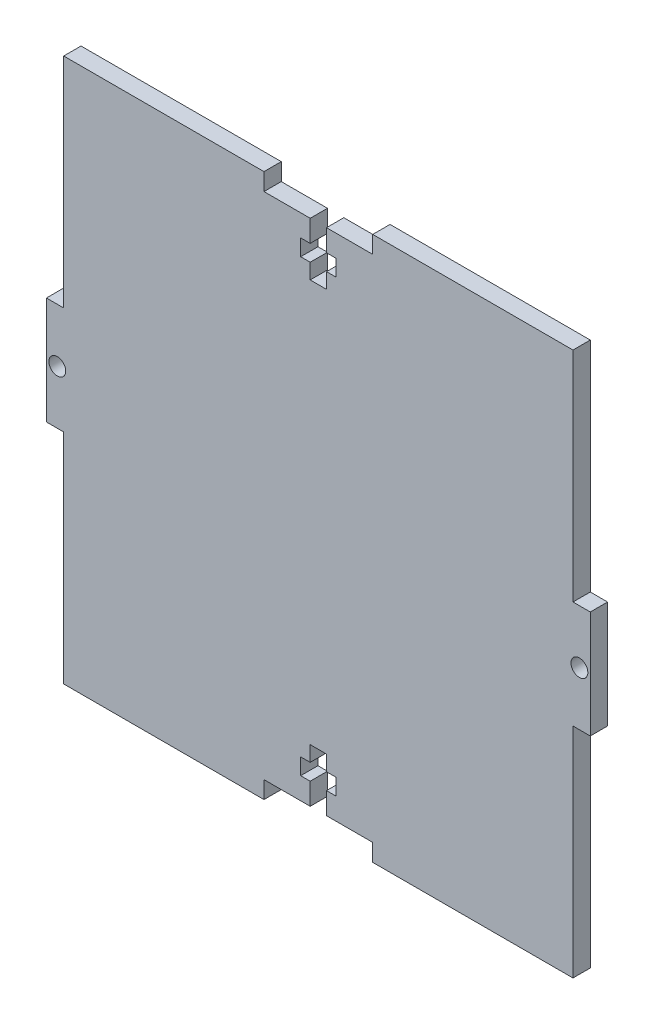
SolidWorks part; units mm, degrees
ref_plane "Front Plane" through (0, 0, 0) normal (0, 0, 1) x (1, 0, 0)
ref_plane "Top Plane" through (0, 0, 0) normal (0, 1, 0) x (1, 0, 0)
ref_plane "Right Plane" through (0, 0, 0) normal (1, 0, 0) x (0, 0, -1)
sketch "Sketch1" plane through (0, 0, 0) normal (0, 0, 1) x (1, 0, 0)
  line L0 (0, 40) -> (0, -40) construction
  line L5 (-50, -50) -> (50, 50) construction
  line L6 (-50, 50) -> (50, -50) construction
  line L7 (-100, 0) -> (100, 0) construction
  line L32 (-50, 50) -> (50, 50)
  line L35 (50, 50) -> (50, -50)
  line L36 (50, -50) -> (-50, -50)
  line L37 (-50, -50) -> (-50, 50)
  point P0 (0, 0)
  dimension "D1" = 100
  dimension "D2" = 100
extrude "Boss-Extrude2" add sketch "Sketch1" along normal blind 3.18
sketch "Sketch2" plane through (0, 0, 3.18) normal (0, 0, 1) x (1, 0, 0)
  line L0 (0, -50) -> (0, 50) construction
  line L1 (-123.0225, 0) -> (147.0753, 0) construction
  line L2 (50, 50) -> (-50, 50) construction
  line L4 (-10, 50) -> (-10, 46.82)
  line L5 (-10, 46.82) -> (-1.5, 46.82)
  line L6 (10, 50) -> (10, 46.82)
  line L7 (1.5, 46.82) -> (10, 46.82)
  line L9 (-1.5, 46.82) -> (-1.5, 42.82)
  line L10 (-1.5, 37) -> (1.5, 37)
  line L11 (1.5, 46.82) -> (1.5, 42.82)
  line L12 (-3.25, 42.82) -> (-1.5, 42.82)
  line L13 (-3.25, 42.82) -> (-3.25, 39.82)
  line L14 (-3.25, 39.82) -> (-1.5, 39.82)
  line L15 (3.25, 42.82) -> (3.25, 39.82)
  line L16 (1.5, 42.82) -> (3.25, 42.82)
  line L17 (-1.5, 39.82) -> (-1.5, 37)
  line L18 (1.5, 39.82) -> (1.5, 37)
  line L19 (1.5, 39.82) -> (3.25, 39.82)
  line L20 (-10, 50) -> (10, 50)
  line L21 (-50, -50) -> (50, -50) construction
  line L22 (-50, 50) -> (-50, -50) construction
  line L23 (-50, 9.875) -> (-46.82, 9.875)
  line L24 (-50, 9.875) -> (-50, 50)
  line L25 (-50, 50) -> (-46.82, 50)
  line L26 (-46.82, 9.875) -> (-46.82, 50)
  line L28 (-50, -9.875) -> (-46.82, -9.875)
  line L29 (-50, -9.875) -> (-50, -50)
  line L30 (-50, -50) -> (-46.82, -50)
  line L31 (-46.82, -9.875) -> (-46.82, -50)
  circle A0 centre (-48, 0) radius 1.55
  dimension "D11" = 3.1
  dimension "D12" = 2
  dimension "D1" = 4
  dimension "D2" = 3
  dimension "D3" = 3
  dimension "D4" = 20
  dimension "D5" = 6.5
  dimension "D6" = 3.18
  dimension "D7" = 13
  dimension "D8" = 19.75
  dimension "D9" = 3.18
  dimension "D10" = 3.18
extrude "Cut-Extrude1" cut sketch "Sketch2" against normal through all
mirror "Mirror1" about plane through (0, 0, 0) normal (0, 1, 0) of "Cut-Extrude1"
mirror "Mirror3" about plane through (0, 0, 0) normal (1, 0, 0) of "Cut-Extrude1"
